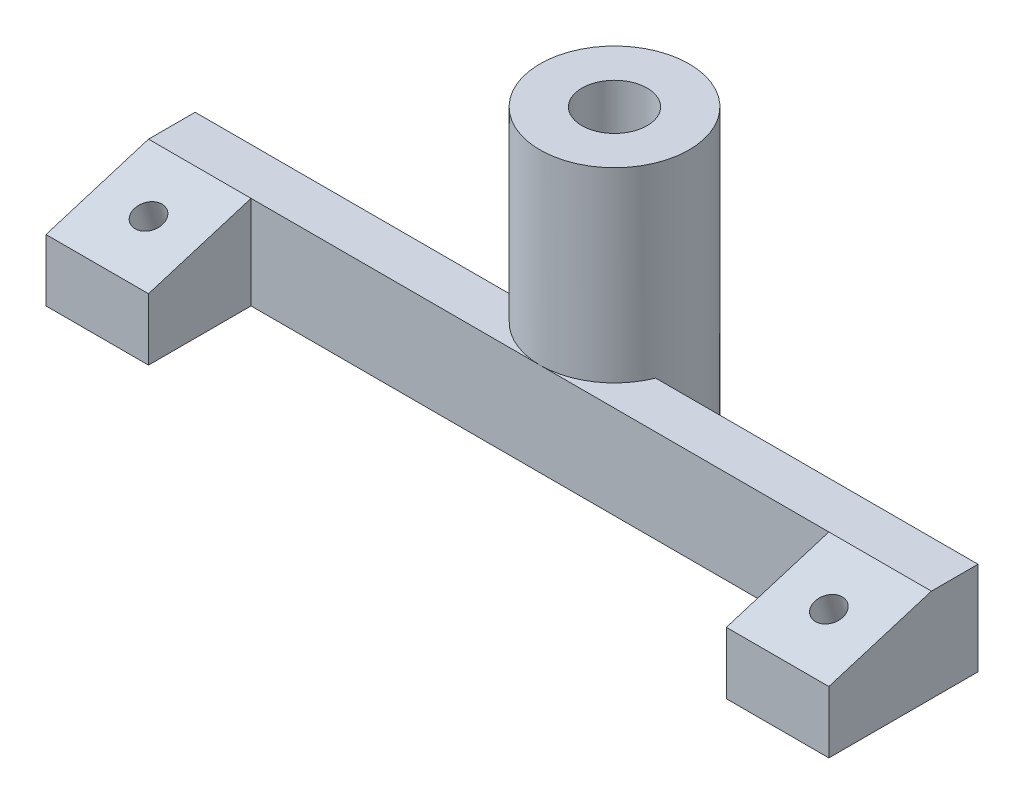
SolidWorks part; units mm, degrees
ref_plane "前视基准面" through (0, 0, 0) normal (0, 0, 1) x (1, 0, 0)
ref_plane "上视基准面" through (0, 0, 0) normal (0, 1, 0) x (1, 0, 0)
ref_plane "右视基准面" through (0, 0, 0) normal (1, 0, 0) x (0, 0, -1)
other "Configuration Table"
sketch "草图1" plane through (0, 0, 0) normal (0, 1, 0) x (1, 0, 0)
  line L0 (-42, 5.5) -> (-42, 10.5)
  line L1 (-31, 5.5) -> (31, 5.5)
  line L2 (-42, 5.5) -> (-42, -5.5)
  line L3 (-42, -5.5) -> (-31, -5.5)
  line L4 (42, 5.5) -> (42, -5.5)
  line L5 (-42, 5.5) -> (42, -5.5) construction
  line L6 (-42, -5.5) -> (42, 5.5) construction
  line L8 (-42, 10.5) -> (42, 10.5)
  line L9 (42, 10.5) -> (42, 5.5)
  line L12 (-31, 5.5) -> (-31, -5.5)
  line L13 (31, -5.5) -> (42, -5.5)
  line L14 (31, 5.5) -> (31, -5.5)
  point P0 (0, 0)
extrude "凸台-拉伸1" add sketch "草图1" along normal blind 10
sketch "草图5" plane through (-42, 0, 0) normal (-1, 0, 0) x (0, 0, 1)
  line L0 (-5.5, 10) -> (5.5, 6.637)
  line L3 (-5.5, 10) -> (5.5, 10)
  line L4 (5.5, 10) -> (5.5, 6.637)
extrude "切除-拉伸4" cut sketch "草图5" against normal through all
sketch "草图6" plane through (0, 12.693, -14.3084) normal (0, -0.9563, -0.2924) x (1, 0, 0)
  circle A2 centre (-36.5, 14.9622) radius 1.5
  circle A3 centre (36.5, 14.9622) radius 1.5
extrude "切除-拉伸5" cut sketch "草图6" along normal through all
ref_plane "基准面2" through (0, 3.7822, 1.1563) normal (0, 0.9563, 0.2924) x (1, 0, 0)
sketch "草图7" plane through (0, 3.7822, 1.1563) normal (0, 0.9563, 0.2924) x (1, 0, 0)
  circle A2 centre (36.5, 2.4321) radius 3.25
  circle A3 centre (-36.5, 2.4321) radius 3.25
extrude "切除-拉伸6" cut sketch "草图7" against normal through all
sketch "草图8" plane through (0, 0, 0) normal (0, -1, 0) x (1, 0, 0)
  circle A0 centre (0, -13.5) radius 8
extrude "凸台-拉伸2" add sketch "草图8" against normal blind 30
sketch "草图9" plane through (0, 30, 0) normal (0, 1, 0) x (1, 0, 0)
  circle A0 centre (0, 13.5) radius 3.5
extrude "切除-拉伸7" cut sketch "草图9" against normal blind 30
sketch "草图10" plane through (0, 0, 0) normal (0, -1, 0) x (1, 0, 0)
  circle A0 centre (0, -13.5) radius 5.25
extrude "切除-拉伸8" cut sketch "草图10" against normal blind 24
